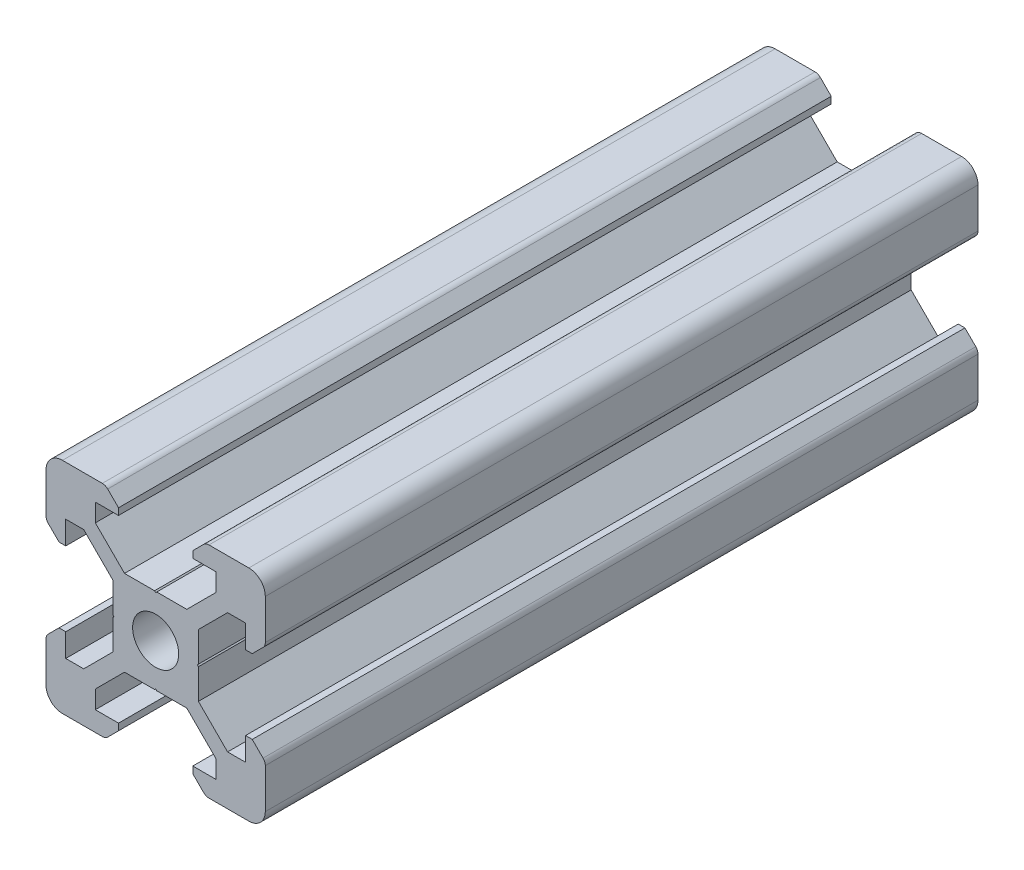
SolidWorks part; units mm, degrees
ref_plane "Front" through (0, 0, 0) normal (0, 0, 1) x (1, 0, 0)
ref_plane "Top" through (0, 0, 0) normal (0, 1, 0) x (1, 0, 0)
ref_plane "Right" through (0, 0, 0) normal (1, 0, 0) x (0, 0, -1)
sketch "Sketch1" plane through (0, 0, 0) normal (0, 0, 1) x (1, 0, 0)
  line L0 (-8.5, 10) -> (-10, 8.5) construction
  line L1 (-8.5, 10) -> (-4.8628, 10)
  line L2 (-10, 8.5) -> (-10, 4.8628)
  line L3 (-8.5, -10) -> (-4.8628, -10)
  line L4 (10, 8.5) -> (10, 4.8628)
  line L5 (-10, 10) -> (10, -10) construction
  line L6 (-10, -10) -> (10, 10) construction
  line L7 (-5.5, -8.2) -> (-3.3865, -8.2)
  line L8 (-8.2, -5.5) -> (-8.2, -3.3865)
  line L9 (-5.5, 8.2) -> (-3.3865, 8.2)
  line L10 (8.2, -5.5) -> (8.2, -3.3865)
  line L11 (-3.9005, 2.8395) -> (-6.561, 5.5)
  line L12 (-6.561, 5.5) -> (-8.2, 5.5)
  line L13 (-2.8395, -3.9005) -> (-0.1, -3.9005)
  line L14 (-3.9005, -2.8395) -> (-3.9005, -0.1)
  line L15 (-2.8395, 3.9005) -> (-0.1, 3.9005)
  line L16 (3.9005, -2.8395) -> (3.9005, -0.1)
  line L17 (-8.2, 3.3865) -> (-8.81, 3.3865)
  line L18 (-8.81, 3.3865) -> (-9.7976, 4.3741)
  line L19 (8.5, 10) -> (10, 8.5) construction
  line L20 (-2.8395, 3.9005) -> (-5.5, 6.561)
  line L21 (-5.5, 6.561) -> (-5.5, 8.2)
  line L22 (-3.3865, 8.2) -> (-3.3865, 8.81)
  line L23 (-3.3865, 8.81) -> (-4.3741, 9.7976)
  line L24 (0, 24.069) -> (0, -33.8154) construction
  line L25 (3.3865, 8.81) -> (4.3741, 9.7976)
  line L26 (3.3865, 8.2) -> (3.3865, 8.81)
  line L27 (5.5, 6.561) -> (5.5, 8.2)
  line L28 (2.8395, 3.9005) -> (5.5, 6.561)
  line L29 (3.3865, 8.2) -> (5.5, 8.2)
  line L30 (4.8628, 10) -> (8.5, 10)
  line L31 (-0.1, 3.9005) -> (0, 3.8005)
  line L32 (0.1, 3.9005) -> (0, 3.8005)
  line L33 (0.1, 3.9005) -> (2.8395, 3.9005)
  line L34 (25.9287, 0) -> (-28.3459, 0) construction
  line L35 (-0.1, -3.9005) -> (0, -3.8005)
  line L36 (0.1, -3.9005) -> (0, -3.8005)
  line L37 (0.1, -3.9005) -> (2.8395, -3.9005)
  line L38 (-3.9005, 0.1) -> (-3.8005, 0)
  line L39 (-3.8005, 0) -> (-3.9005, -0.1)
  line L40 (-3.9005, 0.1) -> (-3.9005, 2.8395)
  line L41 (3.9005, 0.1) -> (3.8005, 0)
  line L42 (3.8005, 0) -> (3.9005, -0.1)
  line L43 (3.9005, 0.1) -> (3.9005, 2.8395)
  line L44 (8.81, 3.3865) -> (9.7976, 4.3741)
  line L45 (8.2, 3.3865) -> (8.81, 3.3865)
  line L46 (6.561, 5.5) -> (8.2, 5.5)
  line L47 (3.9005, 2.8395) -> (6.561, 5.5)
  line L48 (2.8395, -3.9005) -> (5.5, -6.561)
  line L49 (3.9005, -2.8395) -> (6.561, -5.5)
  line L50 (-2.8395, -3.9005) -> (-5.5, -6.561)
  line L51 (-3.9005, -2.8395) -> (-6.561, -5.5)
  line L52 (6.561, -5.5) -> (8.2, -5.5)
  line L53 (-6.561, -5.5) -> (-8.2, -5.5)
  line L54 (-8.81, -3.3865) -> (-9.7976, -4.3741)
  line L55 (-8.2, -3.3865) -> (-8.81, -3.3865)
  line L56 (8.81, -3.3865) -> (9.7976, -4.3741)
  line L57 (8.2, -3.3865) -> (8.81, -3.3865)
  line L58 (8.2, 3.3865) -> (8.2, 5.5)
  line L59 (10, -4.8628) -> (10, -8.5)
  line L60 (-8.2, 3.3865) -> (-8.2, 5.5)
  line L61 (-10, -4.8628) -> (-10, -8.5)
  line L62 (-3.3865, -8.81) -> (-4.3741, -9.7976)
  line L63 (-3.3865, -8.2) -> (-3.3865, -8.81)
  line L64 (3.3865, -8.81) -> (4.3741, -9.7976)
  line L65 (3.3865, -8.2) -> (3.3865, -8.81)
  line L66 (-5.5, -6.561) -> (-5.5, -8.2)
  line L67 (5.5, -6.561) -> (5.5, -8.2)
  line L68 (3.3865, -8.2) -> (5.5, -8.2)
  line L69 (4.8628, -10) -> (8.5, -10)
  circle A0 centre (0, 0) radius 2.1
  arc A1 (-8.5, 10) -> (-10, 8.5) centre (-8.5, 8.5) ccw
  arc A2 (10, 8.5) -> (8.5, 10) centre (8.5, 8.5) ccw
  arc A3 (-4.3741, 9.7976) -> (-4.8628, 10) centre (-4.8628, 9.3088) ccw
  arc A4 (4.8628, 10) -> (4.3741, 9.7976) centre (4.8628, 9.3088) ccw
  arc A5 (-8.5, -10) -> (-10, -8.5) centre (-8.5, -8.5) cw
  arc A6 (9.7976, 4.3741) -> (10, 4.8628) centre (9.3088, 4.8628) ccw
  arc A7 (-10, 4.8628) -> (-9.7976, 4.3741) centre (-9.3088, 4.8628) ccw
  arc A8 (-10, -4.8628) -> (-9.7976, -4.3741) centre (-9.3088, -4.8628) cw
  arc A9 (9.7976, -4.3741) -> (10, -4.8628) centre (9.3088, -4.8628) cw
  arc A10 (10, -8.5) -> (8.5, -10) centre (8.5, -8.5) cw
  arc A11 (-4.3741, -9.7976) -> (-4.8628, -10) centre (-4.8628, -9.3088) cw
  arc A12 (4.8628, -10) -> (4.3741, -9.7976) centre (4.8628, -9.3088) cw
  point P17 (-9.25, 9.25)
  point P21 (9.25, 9.25)
  dimension "D2" = 4.2
  dimension "D4" = 1.5
  dimension "D3" = 20
  dimension "D5" = 0.529
  dimension "D6" = 6.773
  dimension "D7" = 90
  dimension "D8" = 11
  dimension "D9" = 0.61
  dimension "D10" = 0.1
  dimension "D11" = 0.1
  dimension "D12" = 0.1
  dimension "D13" = 0.1
  dimension "D14" = 5.679
  dimension "D15" = 1.639
  dimension "D16" = 1.8
  dimension "D17" = 90
  dimension "D18" = 6.773
  dimension "D19" = 90
extrude "Boss-Extrude1" add sketch "Sketch1" along normal blind 65
